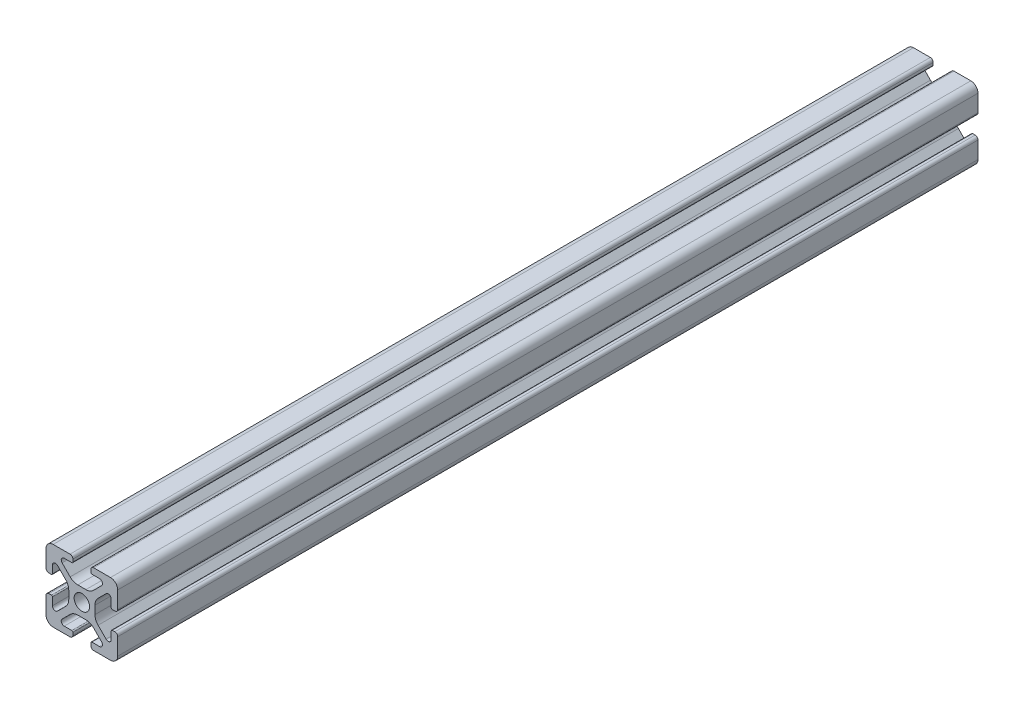
SolidWorks part; units mm, degrees
ref_plane "Front" through (0, 0, 0) normal (0, 0, 1) x (1, 0, 0)
ref_plane "Top" through (0, 0, 0) normal (0, 1, 0) x (1, 0, 0)
ref_plane "Right" through (0, 0, 0) normal (1, 0, 0) x (0, 0, -1)
sketch "Support-Front" plane through (0, 0, 0) normal (0, 0, 1) x (1, 0, 0)
  line L0 (10, 0) -> (-10, 0) construction
  line L1 (-10, -10) -> (10, -10)
  line L2 (-10, -10) -> (-10, 10)
  line L3 (-10, 10) -> (10, 10)
  line L4 (10, -10) -> (10, 10)
  line L5 (0, 10) -> (0, -10) construction
  dimension "Height-Profile" = 20
  dimension "Width-Profile" = 20
sketch "Support-Right-Length" plane through (0, 0, 0) normal (1, 0, 0) x (0, 0, -1)
  line L0 (0, -10) -> (0, 10) construction
  line L1 (-25, 10) -> (25, 10)
  line L2 (-25, 10) -> (-25, -10)
  line L3 (-25, -10) -> (25, -10)
  line L4 (25, 10) -> (25, -10)
  dimension "Length-Profile" = 50
sketch "Support-Profile" plane through (0, 0, 0) normal (0, 0, 1) x (1, 0, 0)
  line L8 (4.9176, -8.2) -> (2.8, -8.2)
  line L9 (2.5, -8.5) -> (2.5, -9.2)
  line L10 (3.3, -10) -> (8, -10)
  line L11 (10, -8) -> (10, -3.3)
  line L24 (9.2, -2.5) -> (8.5, -2.5)
  line L25 (8.2, -2.8) -> (8.2, -4.9176)
  line L26 (6.779, -5.5062) -> (4.5287, -3.2559)
  line L27 (3.65, -1.1346) -> (3.65, 1.1346)
  line L28 (4.5287, 3.2559) -> (6.779, 5.5062)
  line L29 (8.2, 4.9176) -> (8.2, 2.8)
  line L30 (8.5, 2.5) -> (9.2, 2.5)
  line L31 (10, 3.3) -> (10, 8)
  line L32 (8, 10) -> (3.3, 10)
  line L33 (2.5, 9.2) -> (2.5, 8.5)
  line L34 (2.8, 8.2) -> (4.9176, 8.2)
  line L35 (5.5062, 6.779) -> (3.2559, 4.5287)
  line L40 (1.1346, 3.65) -> (-1.1346, 3.65)
  line L41 (-3.2559, 4.5287) -> (-5.5062, 6.779)
  line L42 (-4.9176, 8.2) -> (-2.8, 8.2)
  line L43 (-2.5, 8.5) -> (-2.5, 9.2)
  line L44 (-3.3, 10) -> (-8, 10)
  line L45 (-10, 8) -> (-10, 3.3)
  line L46 (-9.2, 2.5) -> (-8.5, 2.5)
  line L47 (-8.2, 2.8) -> (-8.2, 4.9176)
  line L48 (-6.779, 5.5062) -> (-4.5287, 3.2559)
  line L49 (-3.65, 1.1346) -> (-3.65, -1.1346)
  line L50 (-4.5287, -3.2559) -> (-6.779, -5.5062)
  line L51 (-8.2, -4.9176) -> (-8.2, -2.8)
  line L52 (-8.5, -2.5) -> (-9.2, -2.5)
  line L53 (-10, -3.3) -> (-10, -8)
  line L54 (-8, -10) -> (-3.3, -10)
  line L55 (-2.5, -9.2) -> (-2.5, -8.5)
  line L56 (-2.8, -8.2) -> (-4.9176, -8.2)
  line L57 (-5.5062, -6.779) -> (-3.2559, -4.5287)
  line L58 (-1.1346, -3.65) -> (1.1346, -3.65)
  line L59 (3.2559, -4.5287) -> (5.5062, -6.779)
  circle A2 centre (0, 0) radius 2.15
  arc A3 (2.8, -8.2) -> (2.5, -8.5) centre (2.8, -8.5) ccw
  arc A5 (2.5, -9.2) -> (3.3, -10) centre (3.3, -9.2) ccw
  arc A24 (8, -10) -> (10, -8) centre (8, -8) ccw
  arc A25 (10, -3.3) -> (9.2, -2.5) centre (9.2, -3.3) ccw
  arc A26 (8.5, -2.5) -> (8.2, -2.8) centre (8.5, -2.8) ccw
  arc A27 (6.779, -5.5062) -> (8.2, -4.9176) centre (7.3676, -4.9176) ccw
  arc A28 (3.65, -1.1346) -> (4.5287, -3.2559) centre (6.65, -1.1346) ccw
  arc A29 (4.5287, 3.2559) -> (3.65, 1.1346) centre (6.65, 1.1346) ccw
  arc A30 (8.2, 4.9176) -> (6.779, 5.5062) centre (7.3676, 4.9176) ccw
  arc A31 (8.2, 2.8) -> (8.5, 2.5) centre (8.5, 2.8) ccw
  arc A32 (9.2, 2.5) -> (10, 3.3) centre (9.2, 3.3) ccw
  arc A33 (10, 8) -> (8, 10) centre (8, 8) ccw
  arc A34 (3.3, 10) -> (2.5, 9.2) centre (3.3, 9.2) ccw
  arc A35 (2.5, 8.5) -> (2.8, 8.2) centre (2.8, 8.5) ccw
  arc A38 (5.5062, 6.779) -> (4.9176, 8.2) centre (4.9176, 7.3676) ccw
  arc A39 (1.1346, 3.65) -> (3.2559, 4.5287) centre (1.1346, 6.65) ccw
  arc A44 (-3.2559, 4.5287) -> (-1.1346, 3.65) centre (-1.1346, 6.65) ccw
  arc A45 (-4.9176, 8.2) -> (-5.5062, 6.779) centre (-4.9176, 7.3676) ccw
  arc A46 (-2.8, 8.2) -> (-2.5, 8.5) centre (-2.8, 8.5) ccw
  arc A47 (-2.5, 9.2) -> (-3.3, 10) centre (-3.3, 9.2) ccw
  arc A48 (-8, 10) -> (-10, 8) centre (-8, 8) ccw
  arc A49 (-10, 3.3) -> (-9.2, 2.5) centre (-9.2, 3.3) ccw
  arc A50 (-8.5, 2.5) -> (-8.2, 2.8) centre (-8.5, 2.8) ccw
  arc A51 (-6.779, 5.5062) -> (-8.2, 4.9176) centre (-7.3676, 4.9176) ccw
  arc A52 (-3.65, 1.1346) -> (-4.5287, 3.2559) centre (-6.65, 1.1346) ccw
  arc A53 (-4.5287, -3.2559) -> (-3.65, -1.1346) centre (-6.65, -1.1346) ccw
  arc A54 (-8.2, -4.9176) -> (-6.779, -5.5062) centre (-7.3676, -4.9176) ccw
  arc A55 (-8.2, -2.8) -> (-8.5, -2.5) centre (-8.5, -2.8) ccw
  arc A56 (-9.2, -2.5) -> (-10, -3.3) centre (-9.2, -3.3) ccw
  arc A57 (-10, -8) -> (-8, -10) centre (-8, -8) ccw
  arc A58 (-3.3, -10) -> (-2.5, -9.2) centre (-3.3, -9.2) ccw
  arc A59 (-2.5, -8.5) -> (-2.8, -8.2) centre (-2.8, -8.5) ccw
  arc A60 (-5.5062, -6.779) -> (-4.9176, -8.2) centre (-4.9176, -7.3676) ccw
  arc A61 (-1.1346, -3.65) -> (-3.2559, -4.5287) centre (-1.1346, -6.65) ccw
  arc A62 (3.2559, -4.5287) -> (1.1346, -3.65) centre (1.1346, -6.65) ccw
  arc A63 (4.9176, -8.2) -> (5.5062, -6.779) centre (4.9176, -7.3676) ccw
ref_plane "Ref-Plane-1" through (0, 0, 25) normal (0, 0, 1) x (1, 0, 0)
ref_plane "Ref-Plane-2" through (0, 0, -25) normal (0, 0, 1) x (1, 0, 0)
sketch "Sketch4" plane through (0, 0, 25) normal (0, 0, 1) x (1, 0, 0)
  line L0 (-10, -10) -> (-10, 10) construction
  line L1 (-10, -10) -> (10, -10) construction
  line L2 (10, -10) -> (10, 10) construction
  line L3 (-10, 10) -> (10, 10) construction
  line L4 (-10, -10) -> (-10, 10)
  line L5 (-10, -10) -> (10, -10)
  line L6 (10, -10) -> (10, 10)
  line L7 (-10, 10) -> (10, 10)
extrude "Body" add sketch "Sketch4" against normal blind 240
sketch "Sketch16" plane through (0, 0, 0) normal (0, 0, 1) x (1, 0, 0)
  line L40 (4.9176, -8.2) -> (2.8, -8.2)
  line L41 (2.5, -8.5) -> (2.5, -9.2)
  line L42 (3.3, -10) -> (8, -10)
  line L43 (10, -8) -> (10, -3.3)
  line L44 (9.2, -2.5) -> (8.5, -2.5)
  line L45 (8.2, -2.8) -> (8.2, -4.9176)
  line L46 (6.779, -5.5062) -> (4.5287, -3.2559)
  line L47 (3.65, -1.1346) -> (3.65, 1.1346)
  line L48 (4.5287, 3.2559) -> (6.779, 5.5062)
  line L49 (8.2, 4.9176) -> (8.2, 2.8)
  line L50 (8.5, 2.5) -> (9.2, 2.5)
  line L51 (10, 3.3) -> (10, 8)
  line L52 (8, 10) -> (3.3, 10)
  line L53 (2.5, 9.2) -> (2.5, 8.5)
  line L54 (2.8, 8.2) -> (4.9176, 8.2)
  line L55 (5.5062, 6.779) -> (3.2559, 4.5287)
  line L56 (1.1346, 3.65) -> (-1.1346, 3.65)
  line L57 (-3.2559, 4.5287) -> (-5.5062, 6.779)
  line L58 (-4.9176, 8.2) -> (-2.8, 8.2)
  line L59 (-2.5, 8.5) -> (-2.5, 9.2)
  line L60 (-3.3, 10) -> (-8, 10)
  line L61 (-10, 8) -> (-10, 3.3)
  line L62 (-9.2, 2.5) -> (-8.5, 2.5)
  line L63 (-8.2, 2.8) -> (-8.2, 4.9176)
  line L64 (-6.779, 5.5062) -> (-4.5287, 3.2559)
  line L65 (-3.65, 1.1346) -> (-3.65, -1.1346)
  line L66 (-4.5287, -3.2559) -> (-6.779, -5.5062)
  line L67 (-8.2, -4.9176) -> (-8.2, -2.8)
  line L68 (-8.5, -2.5) -> (-9.2, -2.5)
  line L69 (-10, -3.3) -> (-10, -8)
  line L70 (-8, -10) -> (-3.3, -10)
  line L71 (-2.5, -9.2) -> (-2.5, -8.5)
  line L72 (-2.8, -8.2) -> (-4.9176, -8.2)
  line L73 (-5.5062, -6.779) -> (-3.2559, -4.5287)
  line L74 (-1.1346, -3.65) -> (1.1346, -3.65)
  line L75 (3.2559, -4.5287) -> (5.5062, -6.779)
  line L76 (4.9176, -8.2) -> (2.8, -8.2)
  line L77 (2.5, -8.5) -> (2.5, -9.2)
  line L78 (3.3, -10) -> (8, -10)
  line L79 (10, -8) -> (10, -3.3)
  line L80 (9.2, -2.5) -> (8.5, -2.5)
  line L81 (8.2, -2.8) -> (8.2, -4.9176)
  line L82 (6.779, -5.5062) -> (4.5287, -3.2559)
  line L83 (3.65, -1.1346) -> (3.65, 1.1346)
  line L84 (4.5287, 3.2559) -> (6.779, 5.5062)
  line L85 (8.2, 4.9176) -> (8.2, 2.8)
  line L86 (8.5, 2.5) -> (9.2, 2.5)
  line L87 (10, 3.3) -> (10, 8)
  line L88 (8, 10) -> (3.3, 10)
  line L89 (2.5, 9.2) -> (2.5, 8.5)
  line L90 (2.8, 8.2) -> (4.9176, 8.2)
  line L91 (5.5062, 6.779) -> (3.2559, 4.5287)
  line L92 (1.1346, 3.65) -> (-1.1346, 3.65)
  line L93 (-3.2559, 4.5287) -> (-5.5062, 6.779)
  line L94 (-4.9176, 8.2) -> (-2.8, 8.2)
  line L95 (-2.5, 8.5) -> (-2.5, 9.2)
  line L96 (-3.3, 10) -> (-8, 10)
  line L97 (-10, 8) -> (-10, 3.3)
  line L98 (-9.2, 2.5) -> (-8.5, 2.5)
  line L99 (-8.2, 2.8) -> (-8.2, 4.9176)
  line L100 (-6.779, 5.5062) -> (-4.5287, 3.2559)
  line L101 (-3.65, 1.1346) -> (-3.65, -1.1346)
  line L102 (-4.5287, -3.2559) -> (-6.779, -5.5062)
  line L103 (-8.2, -4.9176) -> (-8.2, -2.8)
  line L104 (-8.5, -2.5) -> (-9.2, -2.5)
  line L105 (-10, -3.3) -> (-10, -8)
  line L106 (-8, -10) -> (-3.3, -10)
  line L107 (-2.5, -9.2) -> (-2.5, -8.5)
  line L108 (-2.8, -8.2) -> (-4.9176, -8.2)
  line L109 (-5.5062, -6.779) -> (-3.2559, -4.5287)
  line L110 (-1.1346, -3.65) -> (1.1346, -3.65)
  line L111 (3.2559, -4.5287) -> (5.5062, -6.779)
  circle A7 centre (0, 0) radius 2.15 construction
  circle A8 centre (0, 0) radius 2.15
  arc A43 (2.8, -8.2) -> (2.5, -8.5) centre (2.8, -8.5) ccw
  arc A44 (2.5, -9.2) -> (3.3, -10) centre (3.3, -9.2) ccw
  arc A45 (8, -10) -> (10, -8) centre (8, -8) ccw
  arc A46 (10, -3.3) -> (9.2, -2.5) centre (9.2, -3.3) ccw
  arc A47 (8.5, -2.5) -> (8.2, -2.8) centre (8.5, -2.8) ccw
  arc A48 (6.779, -5.5062) -> (8.2, -4.9176) centre (7.3676, -4.9176) ccw
  arc A49 (3.65, -1.1346) -> (4.5287, -3.2559) centre (6.65, -1.1346) ccw
  arc A50 (4.5287, 3.2559) -> (3.65, 1.1346) centre (6.65, 1.1346) ccw
  arc A51 (8.2, 4.9176) -> (6.779, 5.5062) centre (7.3676, 4.9176) ccw
  arc A52 (8.2, 2.8) -> (8.5, 2.5) centre (8.5, 2.8) ccw
  arc A53 (9.2, 2.5) -> (10, 3.3) centre (9.2, 3.3) ccw
  arc A54 (10, 8) -> (8, 10) centre (8, 8) ccw
  arc A55 (3.3, 10) -> (2.5, 9.2) centre (3.3, 9.2) ccw
  arc A56 (2.5, 8.5) -> (2.8, 8.2) centre (2.8, 8.5) ccw
  arc A57 (5.5062, 6.779) -> (4.9176, 8.2) centre (4.9176, 7.3676) ccw
  arc A58 (1.1346, 3.65) -> (3.2559, 4.5287) centre (1.1346, 6.65) ccw
  arc A59 (-3.2559, 4.5287) -> (-1.1346, 3.65) centre (-1.1346, 6.65) ccw
  arc A60 (-4.9176, 8.2) -> (-5.5062, 6.779) centre (-4.9176, 7.3676) ccw
  arc A61 (-2.8, 8.2) -> (-2.5, 8.5) centre (-2.8, 8.5) ccw
  arc A62 (-2.5, 9.2) -> (-3.3, 10) centre (-3.3, 9.2) ccw
  arc A63 (-8, 10) -> (-10, 8) centre (-8, 8) ccw
  arc A64 (-10, 3.3) -> (-9.2, 2.5) centre (-9.2, 3.3) ccw
  arc A65 (-8.5, 2.5) -> (-8.2, 2.8) centre (-8.5, 2.8) ccw
  arc A66 (-6.779, 5.5062) -> (-8.2, 4.9176) centre (-7.3676, 4.9176) ccw
  arc A67 (-3.65, 1.1346) -> (-4.5287, 3.2559) centre (-6.65, 1.1346) ccw
  arc A68 (-4.5287, -3.2559) -> (-3.65, -1.1346) centre (-6.65, -1.1346) ccw
  arc A69 (-8.2, -4.9176) -> (-6.779, -5.5062) centre (-7.3676, -4.9176) ccw
  arc A70 (-8.2, -2.8) -> (-8.5, -2.5) centre (-8.5, -2.8) ccw
  arc A71 (-9.2, -2.5) -> (-10, -3.3) centre (-9.2, -3.3) ccw
  arc A72 (-10, -8) -> (-8, -10) centre (-8, -8) ccw
  arc A73 (-3.3, -10) -> (-2.5, -9.2) centre (-3.3, -9.2) ccw
  arc A74 (-2.5, -8.5) -> (-2.8, -8.2) centre (-2.8, -8.5) ccw
  arc A75 (-5.5062, -6.779) -> (-4.9176, -8.2) centre (-4.9176, -7.3676) ccw
  arc A76 (-1.1346, -3.65) -> (-3.2559, -4.5287) centre (-1.1346, -6.65) ccw
  arc A77 (3.2559, -4.5287) -> (1.1346, -3.65) centre (1.1346, -6.65) ccw
  arc A78 (4.9176, -8.2) -> (5.5062, -6.779) centre (4.9176, -7.3676) ccw
  arc A79 (2.8, -8.2) -> (2.5, -8.5) centre (2.8, -8.5) ccw
  arc A80 (2.5, -9.2) -> (3.3, -10) centre (3.3, -9.2) ccw
  arc A81 (8, -10) -> (10, -8) centre (8, -8) ccw
  arc A82 (10, -3.3) -> (9.2, -2.5) centre (9.2, -3.3) ccw
  arc A83 (8.5, -2.5) -> (8.2, -2.8) centre (8.5, -2.8) ccw
  arc A84 (6.779, -5.5062) -> (8.2, -4.9176) centre (7.3676, -4.9176) ccw
  arc A85 (3.65, -1.1346) -> (4.5287, -3.2559) centre (6.65, -1.1346) ccw
  arc A86 (4.5287, 3.2559) -> (3.65, 1.1346) centre (6.65, 1.1346) ccw
  arc A87 (8.2, 4.9176) -> (6.779, 5.5062) centre (7.3676, 4.9176) ccw
  arc A88 (8.2, 2.8) -> (8.5, 2.5) centre (8.5, 2.8) ccw
  arc A89 (9.2, 2.5) -> (10, 3.3) centre (9.2, 3.3) ccw
  arc A90 (10, 8) -> (8, 10) centre (8, 8) ccw
  arc A91 (3.3, 10) -> (2.5, 9.2) centre (3.3, 9.2) ccw
  arc A92 (2.5, 8.5) -> (2.8, 8.2) centre (2.8, 8.5) ccw
  arc A93 (5.5062, 6.779) -> (4.9176, 8.2) centre (4.9176, 7.3676) ccw
  arc A94 (1.1346, 3.65) -> (3.2559, 4.5287) centre (1.1346, 6.65) ccw
  arc A95 (-3.2559, 4.5287) -> (-1.1346, 3.65) centre (-1.1346, 6.65) ccw
  arc A96 (-4.9176, 8.2) -> (-5.5062, 6.779) centre (-4.9176, 7.3676) ccw
  arc A97 (-2.8, 8.2) -> (-2.5, 8.5) centre (-2.8, 8.5) ccw
  arc A98 (-2.5, 9.2) -> (-3.3, 10) centre (-3.3, 9.2) ccw
  arc A99 (-8, 10) -> (-10, 8) centre (-8, 8) ccw
  arc A100 (-10, 3.3) -> (-9.2, 2.5) centre (-9.2, 3.3) ccw
  arc A101 (-8.5, 2.5) -> (-8.2, 2.8) centre (-8.5, 2.8) ccw
  arc A102 (-6.779, 5.5062) -> (-8.2, 4.9176) centre (-7.3676, 4.9176) ccw
  arc A103 (-3.65, 1.1346) -> (-4.5287, 3.2559) centre (-6.65, 1.1346) ccw
  arc A104 (-4.5287, -3.2559) -> (-3.65, -1.1346) centre (-6.65, -1.1346) ccw
  arc A105 (-8.2, -4.9176) -> (-6.779, -5.5062) centre (-7.3676, -4.9176) ccw
  arc A106 (-8.2, -2.8) -> (-8.5, -2.5) centre (-8.5, -2.8) ccw
  arc A107 (-9.2, -2.5) -> (-10, -3.3) centre (-9.2, -3.3) ccw
  arc A108 (-10, -8) -> (-8, -10) centre (-8, -8) ccw
  arc A109 (-3.3, -10) -> (-2.5, -9.2) centre (-3.3, -9.2) ccw
  arc A110 (-2.5, -8.5) -> (-2.8, -8.2) centre (-2.8, -8.5) ccw
  arc A111 (-5.5062, -6.779) -> (-4.9176, -8.2) centre (-4.9176, -7.3676) ccw
  arc A112 (-1.1346, -3.65) -> (-3.2559, -4.5287) centre (-1.1346, -6.65) ccw
  arc A113 (3.2559, -4.5287) -> (1.1346, -3.65) centre (1.1346, -6.65) ccw
  arc A114 (4.9176, -8.2) -> (5.5062, -6.779) centre (4.9176, -7.3676) ccw
  dimension "D1" = 0
extrude "Cut-Profile" cut sketch "Sketch16" against normal through all and the other way through all flip side to cut
